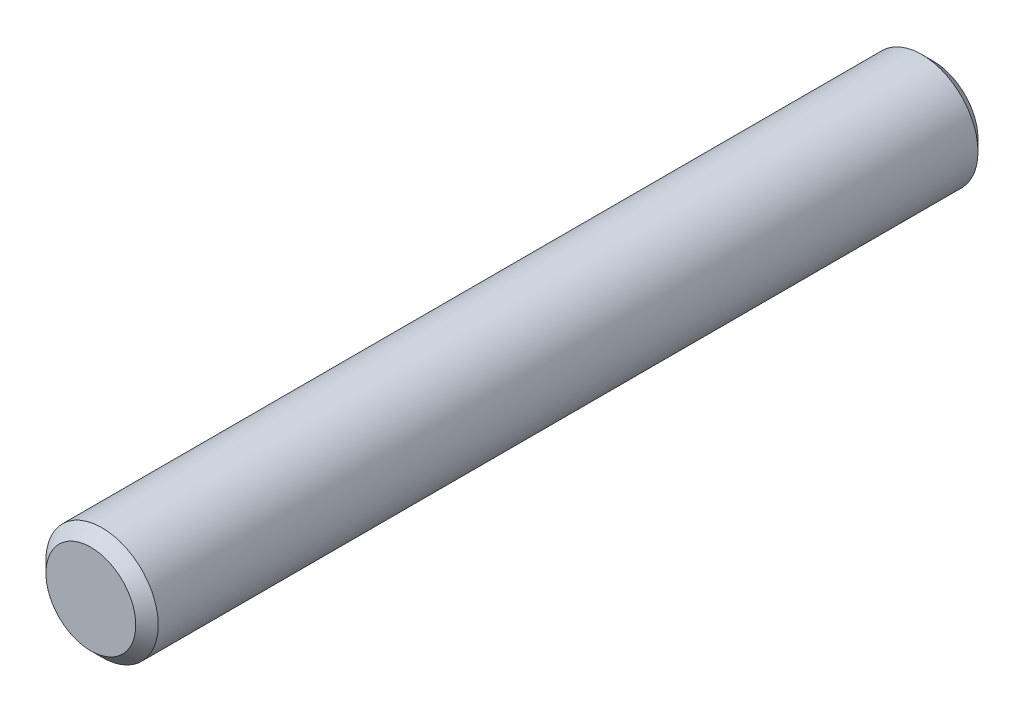
SolidWorks part; units mm, degrees
ref_plane "前视基准面" through (0, 0, 0) normal (0, 0, 1) x (1, 0, 0)
ref_plane "上视基准面" through (0, 0, 0) normal (0, 1, 0) x (1, 0, 0)
ref_plane "右视基准面" through (0, 0, 0) normal (1, 0, 0) x (0, 0, -1)
sketch "草图1" plane through (0, 0, 0) normal (0, 0, 1) x (1, 0, 0)
  circle A0 centre (0, 0) radius 1
  dimension "D1" = 2
extrude "凸台-拉伸1" add sketch "草图1" along normal mid plane 15
chamfer "倒角1" distance 0.2 angle 45 2 edges at (1, 0, -7.5) (1, 0, 7.5)
